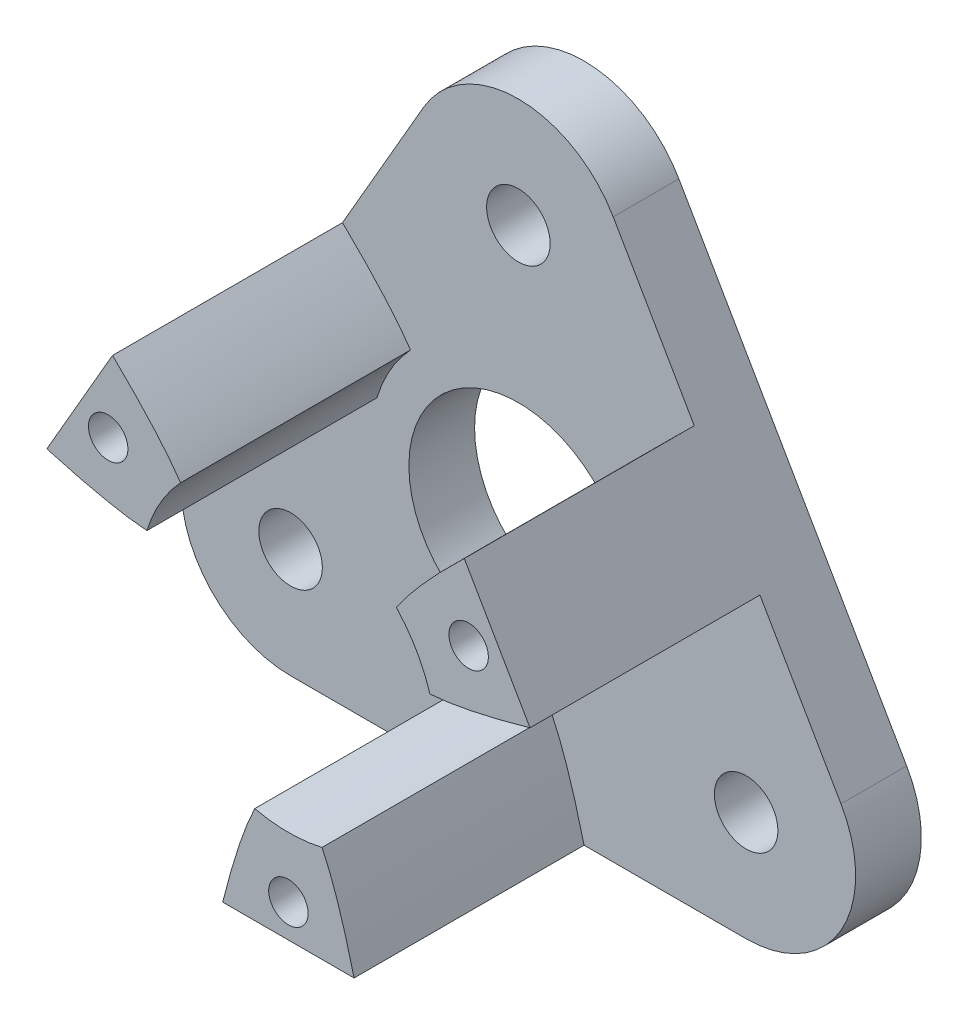
SolidWorks part; units mm, degrees
ref_plane "Front Plane" through (0, 0, 0) normal (0, 0, 1) x (1, 0, 0)
ref_plane "Top Plane" through (0, 0, 0) normal (0, 1, 0) x (1, 0, 0)
ref_plane "Right Plane" through (0, 0, 0) normal (1, 0, 0) x (0, 0, -1)
sketch "Sketch1" plane through (0, 0, 0) normal (0, 0, 1) x (1, 0, 0)
  line L0 (0, 12.0089) -> (0, 0) construction
  line L1 (0, 0) -> (-10.4, -6.0044) construction
  line L2 (0, 0) -> (10.4, -6.0044) construction
  line L3 (-14.7301, -3.5044) -> (-4.3301, 14.5089)
  line L4 (4.3301, 14.5089) -> (14.7301, -3.5044)
  line L5 (10.4, -11.0044) -> (-10.4, -11.0044)
  line L6 (0, 12.0089) -> (10.4, -6.0044) construction
  line L7 (10.4, -6.0044) -> (-10.4, -6.0044) construction
  line L8 (-10.4, -6.0044) -> (0, 12.0089) construction
  circle A0 centre (0, 12.0089) radius 1.45
  circle A1 centre (-10.4, -6.0044) radius 1.45
  circle A2 centre (10.4, -6.0044) radius 1.45
  arc A4 (4.3301, 14.5089) -> (-4.3301, 14.5089) centre (0, 12.0089) ccw
  arc A5 (-14.7301, -3.5044) -> (-10.4, -11.0044) centre (-10.4, -6.0044) ccw
  arc A6 (10.4, -11.0044) -> (14.7301, -3.5044) centre (10.4, -6.0044) ccw
  circle A7 centre (0, 0) radius 5
  spline S0 degree 3 poles (12.0715, -6.9088) (-10.7674, -6.2165) (0.0526, 13.9086) (12.0715, -6.9088) (-10.7674, -6.2165) (0.0526, 13.9086) knots -1 -0.674106 -0.325894 0 0.325894 0.674106 1 1.325894 1.674106 2 only from (-5.2828, -3.05) to (-5.2828, -3.05) construction
  dimension "D4" = 2.9
  dimension "D5" = 10
  dimension "D6" = 10
  dimension "D1" = 20.8
  dimension "D2" = 120
  dimension "D3" = 120
extrude "Boss-Extrude1" add sketch "Sketch1" along normal blind 3
sketch "Sketch2" plane through (0, 0, 3) normal (0, 0, 1) x (1, 0, 0)
  line L0 (9.5301, 5.5022) -> (4.3301, 2.5) construction
  line L1 (14.7301, -3.5044) -> (4.3301, 14.5089) construction
  line L2 (8.0301, 8.1003) -> (11.0301, 2.9041)
  line L6 (3, -11.0044) -> (-3, -11.0044)
  line L8 (-11.0301, 2.9041) -> (-8.0301, 8.1003)
  line L9 (3, -10.625) -> (-3, -10.625) [skipped]
  line L10 (-10.7015, 3.0939) -> (-7.7015, 8.29) [skipped]
  line L11 (0, -10.625) -> (0, -4.6206) construction
  line L12 (-9.2015, 5.6919) -> (-4.0015, 2.6897) construction
  circle A0 centre (0, 12.0089) radius 6 construction
  circle A1 centre (10.4, -6.0044) radius 6 construction
  circle A2 centre (0, 0) radius 5 construction
  spline S0 degree 2 poles (8.0301, 8.1003) (-0.8699, -0.5022) (11.0301, 2.9041) knots 0 0 0 1 1 1
  spline S1 degree 2 poles (3, -11.0044) (0, 1.0044) (-3, -11.0044) knots 0 0 0 1 1 1
  spline S2 degree 2 poles (-11.0301, 2.9041) (0.8699, -0.5022) (-8.0301, 8.1003) knots 0 0 0 1 1 1
  point P14 (9.5301, 5.5022)
  point P15 (-9.2015, 5.6919)
  point P17 (0, -10.625)
  point P27 (0, 0)
  dimension "D1" = 12
  dimension "D2" = 12
  dimension "D3" = 6
  dimension "D4" = 0
  dimension "D5" = 3
  dimension "D6" = 3
extrude "Boss-Extrude2" add sketch "Sketch2" along normal blind 10.5
sketch "Sketch3" plane through (0, 0, 3) normal (0, 0, 1) x (1, 0, 0)
  circle A0 centre (0, 0) radius 6.75
  dimension "D1" = 13.5
extrude "Cut-Extrude1" cut sketch "Sketch3" along normal through all
sketch "Sketch4" plane through (0, 0, 13.5) normal (0, 0, 1) x (1, 0, 0)
  line L0 (9.5301, 5.5022) -> (6.9282, 4) construction
  line L1 (11.0301, 2.9041) -> (8.0301, 8.1003) construction
  circle A12 centre (0, 0) radius 8 construction
  circle A15 centre (8.2292, 4.7511) radius 0.9
  circle A18 centre (0, -9.5022) radius 0.9
  circle A19 centre (-8.2292, 4.7511) radius 0.9
  point P14 (0, 0)
extrude "Cut-Extrude2" cut sketch "Sketch4" against normal through all
sketch "Sketch5" plane through (0, 0, 3) normal (0, 0, 1) x (1, 0, 0)
  circle A0 centre (0, 0) radius 6.75
  circle A1 centre (-10.4, -6.0044) radius 5.2589
  dimension "D1" = 13.5
  dimension "D2" = 10.5178
